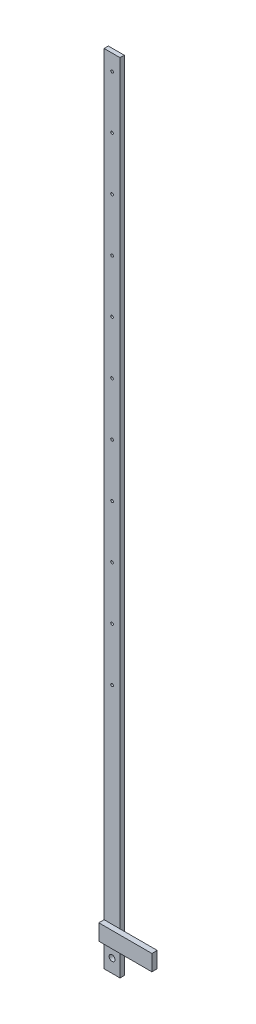
SolidWorks part; units mm, degrees
ref_plane "Ön Düzlem" through (0, 0, 0) normal (0, 0, 1) x (1, 0, 0)
ref_plane "Üst Düzlem" through (0, 0, 0) normal (0, 1, 0) x (1, 0, 0)
ref_plane "Sağ Düzlem" through (0, 0, 0) normal (1, 0, 0) x (0, 0, -1)
sketch "Sketch1" plane through (0, 0, 0) normal (0, 0, 1) x (1, 0, 0)
  line L1 (-1.5, -2.5) -> (1.5, -2.5)
  line L2 (-1.5, -2.5) -> (-1.5, 147.5)
  line L3 (-1.5, 147.5) -> (1.5, 147.5)
  line L4 (1.5, -2.5) -> (1.5, 147.5)
  circle A0 centre (0, 0) radius 0.55
  circle A1 centre (0, 144.5) radius 0.25
  circle A2 centre (0, 134.5) radius 0.25
  circle A3 centre (0, 124.5) radius 0.25
  circle A4 centre (0, 114.5) radius 0.25
  circle A5 centre (0, 104.5) radius 0.25
  circle A6 centre (0, 64.5) radius 0.25
  circle A7 centre (0, 54.5) radius 0.25
  circle A8 centre (0, 94.5) radius 0.25
  circle A9 centre (0, 84.5) radius 0.25
  circle A10 centre (0, 74.5) radius 0.25
  circle A11 centre (0, 44.5) radius 0.25
  point P31 (-0.4064, 62.8209)
  dimension "D1" = 1.5
  dimension "D4" = 3
  dimension "D12" = 1.1
  dimension "D13" = 0.5
  dimension "D14" = 0.5
  dimension "D16" = 0.5
  dimension "D17" = 0.5
  dimension "D18" = 0.5
  dimension "D19" = 0.5
  dimension "D20" = 0.5
  dimension "D21" = 0.5
  dimension "D23" = 10
  dimension "D26" = 0.5
  dimension "D27" = 0.5
  dimension "D28" = 0.5
  dimension "D2" = 1.5
  dimension "D3" = 2.5
  dimension "D5" = 10
  dimension "D6" = 10
  dimension "D7" = 10
  dimension "D8" = 10
  dimension "D9" = 10
  dimension "D10" = 10
  dimension "D11" = 10
  dimension "D15" = 1.5
  dimension "D22" = 150
  dimension "D24" = 10
  dimension "D25" = 10
extrude "Boss-Extrude3" add sketch "Sketch1" along normal blind 0.8
sketch "Sketch2" plane through (0, 0, 0.8) normal (0, 0, 1) x (1, 0, 0)
  line L0 (-1.5, 147.5) -> (-1.5, -2.5) construction
  line L1 (-1.5, 5.5) -> (8.5, 5.5)
  line L2 (-1.5, 5.5) -> (-1.5, 2.5)
  line L3 (-1.5, 2.5) -> (8.5, 2.5)
  line L4 (8.5, 5.5) -> (8.5, 2.5)
  dimension "D1" = 10
  dimension "D2" = 5
  dimension "D3" = 3
extrude "Boss-Extrude4" add sketch "Sketch2" along normal blind 1
